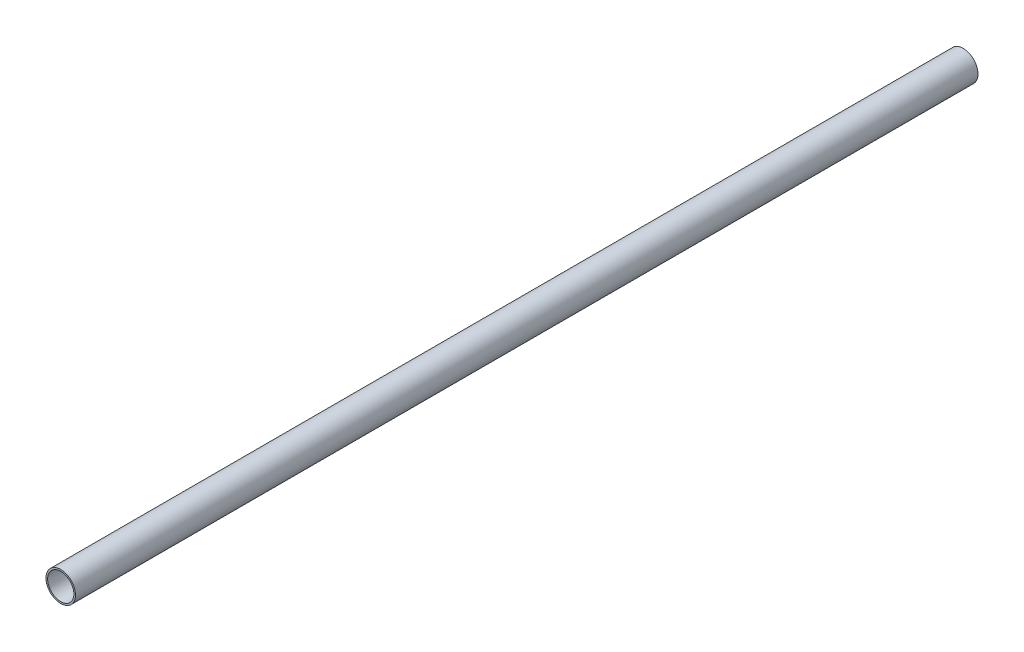
SolidWorks part; units mm, degrees
material "Carbon Fiber Tube - UD Approx"
ref_plane "Front Plane" through (0, 0, 0) normal (0, 0, 1) x (1, 0, 0)
ref_plane "Top Plane" through (0, 0, 0) normal (0, 1, 0) x (1, 0, 0)
ref_plane "Right Plane" through (0, 0, 0) normal (1, 0, 0) x (0, 0, -1)
sketch "Sketch1" plane through (0, 0, 0) normal (0, 0, 1) x (1, 0, 0)
  circle A0 centre (0, 0) radius 9
  circle A1 centre (0, 0) radius 8
  dimension "D1" = 18
  dimension "D2" = 16
extrude "Boss-Extrude1" add sketch "Sketch1" along normal blind 550
sketch "Sketch3" plane through (0, 0, 0) normal (1, 0, 0) x (0, 0, -1)
  line L0 (0, 0) -> (-550, 0) construction
  line L1 (-550, 9) -> (-550, -9) construction
